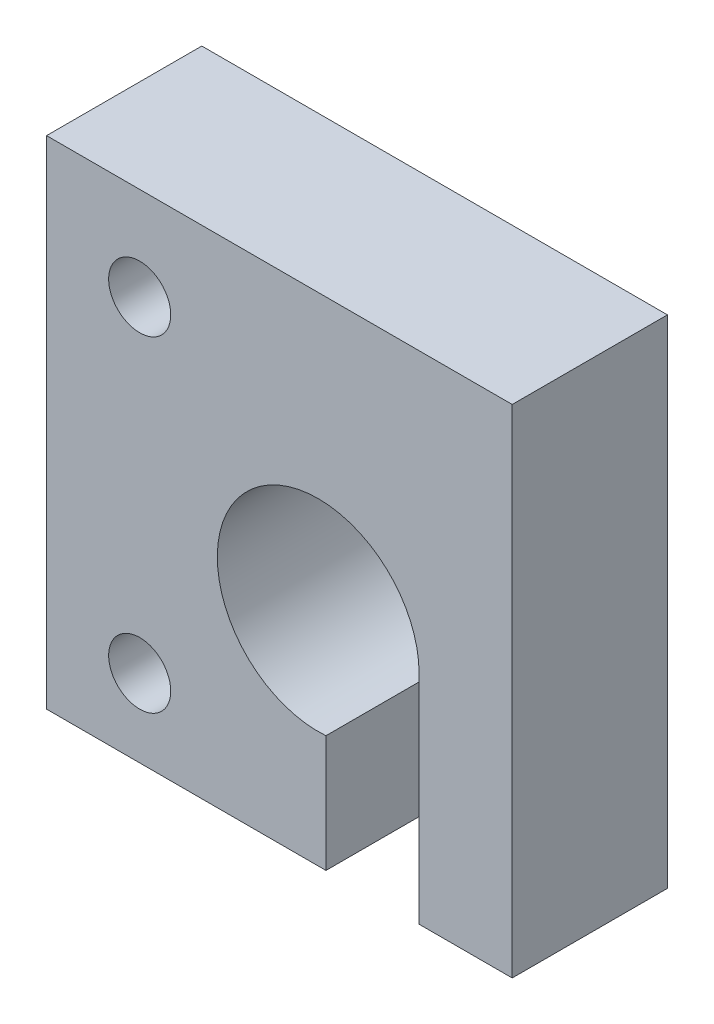
SolidWorks part; units mm, degrees
ref_plane "Спереди" through (0, 0, 0) normal (0, 0, 1) x (1, 0, 0)
ref_plane "Сверху" through (0, 0, 0) normal (0, 1, 0) x (1, 0, 0)
ref_plane "Справа" through (0, 0, 0) normal (1, 0, 0) x (0, 0, -1)
sketch "Эскиз2" plane through (0, 0, 0) normal (0, 0, 1) x (1, 0, 0)
  line L0 (6.5, 0) -> (6.5, -14)
  line L1 (6.5, -14) -> (12.5, -14)
  line L2 (0.5, -14) -> (0.5, -6.4807)
  line L3 (12.5, -14) -> (12.5, 18)
  line L4 (12.5, 18) -> (-17.5, 18)
  line L5 (-17.5, 18) -> (-17.5, -14)
  line L6 (-17.5, -14) -> (0.5, -14)
  line L7 (-11.5, 18) -> (-11.5, -14) construction
  arc A0 (6.5, 0) -> (0.5, -6.4807) centre (0, 0) ccw
  circle A1 centre (-11.5, 12) radius 2
  circle A2 centre (-11.5, -9) radius 2
  point P11 (0.5, -10.2404)
  dimension "D1" = 6.5
  dimension "D8" = 6
  dimension "D9" = 5
  dimension "D7" = 4
  dimension "D2" = 14
  dimension "D3" = 6
  dimension "D4" = 6
  dimension "D5" = 32
  dimension "D6" = 30
  dimension "D10" = 6
extrude "Бобышка-Вытянуть1" add sketch "Эскиз2" along normal blind 10
